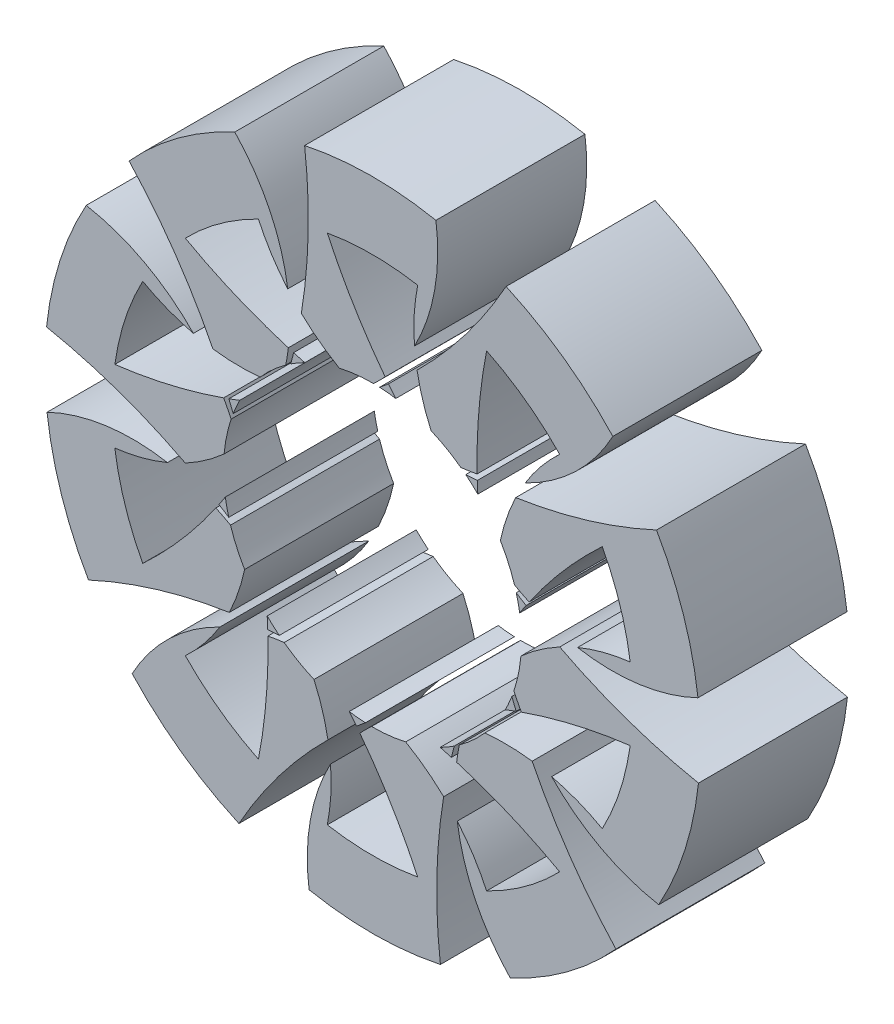
SolidWorks part; units mm, degrees
ref_plane "Front Plane" through (0, 0, 0) normal (0, 0, 1) x (1, 0, 0)
ref_plane "Top Plane" through (0, 0, 0) normal (0, 1, 0) x (1, 0, 0)
ref_plane "Right Plane" through (0, 0, 0) normal (1, 0, 0) x (0, 0, -1)
sketch "Sketch1" plane through (0, 0, 0) normal (0, 0, 1) x (1, 0, 0)
  circle A0 centre (0, 0) radius 6
  circle A1 centre (0, 0) radius 13.2
extrude "Boss-Extrude1" add sketch "Sketch1" along normal blind 6
sketch "Sketch2" plane through (0, 0, 6) normal (0, 0, 1) x (1, 0, 0)
  line L0 (0, 0) -> (0, 15.2) construction
  line L1 (-1.8199, 15.2) -> (0, 0) construction
  line L2 (1.8199, 15.2) -> (0, 0) construction
  arc A0 (-2.8199, 12.8953) -> (2.8199, 12.8953) centre (0, 0) cw
  arc A1 (11.9474, -1.1225) -> (11.9474, 1.1225) centre (0, 0) cw
  arc A2 (-1.8199, 10.32) -> (1.8199, 10.32) centre (0, 0) cw
  arc A3 (-2.8199, 12.8953) -> (-1.8199, 10.32) centre (17.1836, 19.1809) cw
  arc A4 (2.8199, 12.8953) -> (1.8199, 10.32) centre (9.6459, 8.7629) cw
extrude "Cut-Extrude1" cut sketch "Sketch2" against normal through all contours A0 A4 A2 A3
pattern_circular "CirPattern1" count 10 over 360 about axis through (0, 0, 0) along (0, 0, 1) of "Cut-Extrude1"
